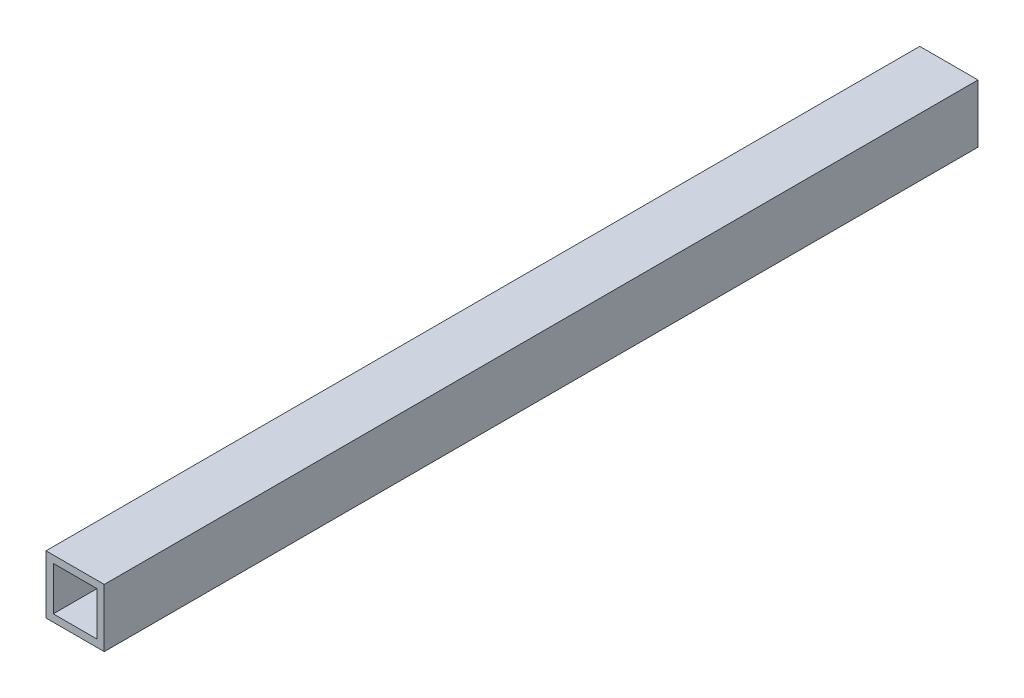
SolidWorks part; units mm, degrees
material "AISI 302"
ref_plane "Front" through (0, 0, 0) normal (0, 0, 1) x (1, 0, 0)
ref_plane "Top" through (0, 0, 0) normal (0, 1, 0) x (1, 0, 0)
ref_plane "Right" through (0, 0, 0) normal (1, 0, 0) x (0, 0, -1)
sketch "Sketch1" plane through (0, 0, 0) normal (0, 0, 1) x (1, 0, 0)
  line L1 (0, 0) -> (203.2, 0)
  line L2 (0, 0) -> (0, 203.2)
  line L3 (0, 203.2) -> (203.2, 203.2)
  line L4 (203.2, 0) -> (203.2, 203.2)
  dimension "D1" = 203.2
  dimension "D2" = 203.2
extrude "Boss-Extrude1" add sketch "Sketch1" against normal blind 3048
sketch "Sketch3" plane through (0, 0, 0) normal (0, 0, 1) x (1, 0, 0)
  line L0 (203.2, 203.2) -> (0, 203.2) construction
  line L1 (25.4, 25.4) -> (177.8, 25.4)
  line L2 (25.4, 25.4) -> (25.4, 177.8)
  line L3 (25.4, 177.8) -> (177.8, 177.8)
  line L4 (177.8, 25.4) -> (177.8, 177.8)
  line L5 (203.2, 0) -> (203.2, 203.2) construction
  line L6 (0, 0) -> (203.2, 0) construction
  line L7 (0, 203.2) -> (0, 0) construction
  dimension "D1" = 25.4
  dimension "D2" = 25.4
  dimension "D3" = 25.4
  dimension "D4" = 25.4
extrude "Cut-Extrude1" cut sketch "Sketch3" against normal blind 2438.4
